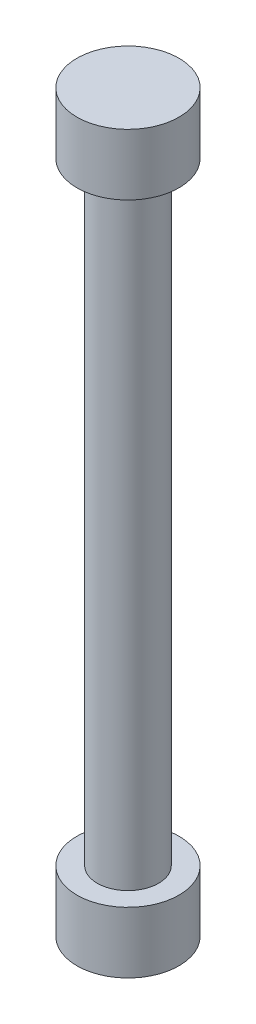
SolidWorks part; units mm, degrees
material "AISI 304"
ref_plane "Front Plane" through (0, 0, 0) normal (0, 0, 1) x (1, 0, 0)
ref_plane "Top Plane" through (0, 0, 0) normal (0, 1, 0) x (1, 0, 0)
ref_plane "Right Plane" through (0, 0, 0) normal (1, 0, 0) x (0, 0, -1)
sketch "Sketch1" plane through (0, 0, 0) normal (0, 1, 0) x (1, 0, 0)
  circle A0 centre (0, 0) radius 0.9525
  dimension "D1" = 1.905
extrude "Boss-Extrude1" add sketch "Sketch1" along normal blind 9.525
sketch "Sketch2" plane through (0, 9.525, 0) normal (0, 1, 0) x (1, 0, 0)
  circle A0 centre (0, 0) radius 1.5875
  dimension "D1" = 3.175
extrude "Boss-Extrude2" add sketch "Sketch2" along normal blind 1.905
mirror "Mirror1" about plane through (0, 0, 0) normal (0, 1, 0) of "Boss-Extrude2", "Boss-Extrude1"
